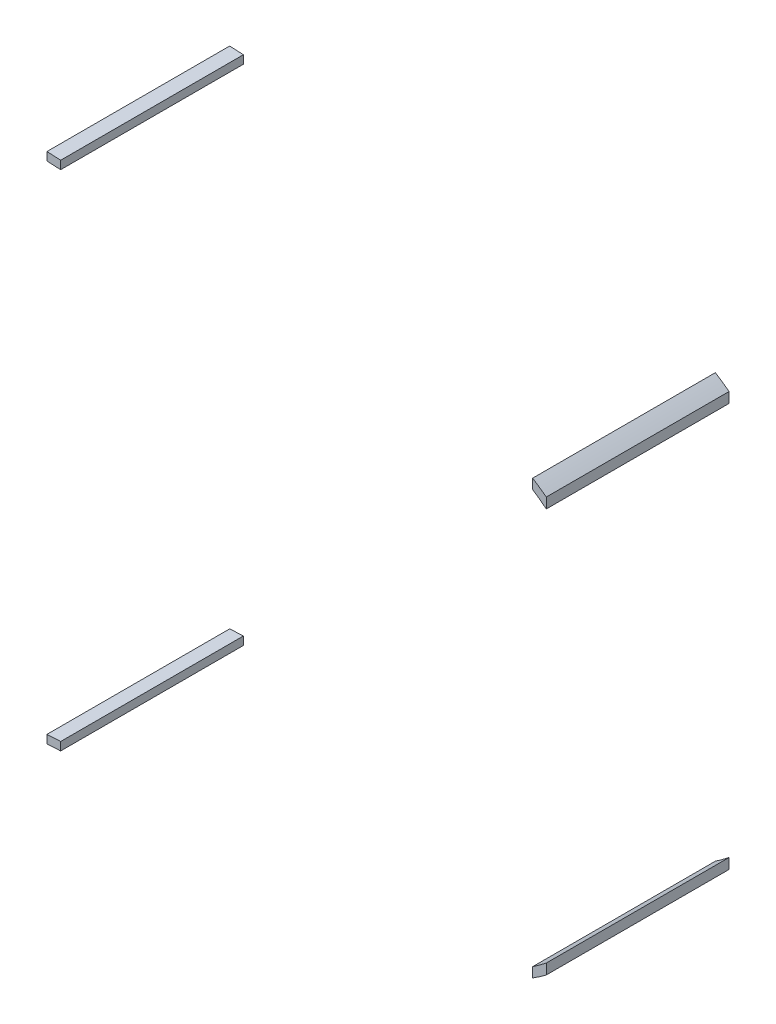
SolidWorks part; units mm, degrees
ref_plane "Front Plane" through (0, 0, 0) normal (0, 0, 1) x (1, 0, 0)
ref_plane "Top Plane" through (0, 0, 0) normal (0, 1, 0) x (1, 0, 0)
ref_plane "Right Plane" through (0, 0, 0) normal (1, 0, 0) x (0, 0, -1)
sketch "Sketch2" plane through (0, 0, 0) normal (0, 0, 1) x (1, 0, 0)
  line L7 (123.1026, -49.6697) -> (123.1026, -51.8155)
  line L19 (123.1026, 40.7834) -> (123.1026, 42.9292)
  line L20 (126.1026, 40.8584) -> (126.1026, 38.5895)
  line L21 (19.8026, -58.631) -> (19.8026, -60.4333)
  line L22 (19.8026, 49.7448) -> (16.8026, 49.8964)
  line L23 (19.8026, 49.7448) -> (19.8026, 51.5471)
  line L24 (16.8026, 51.6987) -> (19.8026, 51.5471)
  line L29 (16.8026, -58.7826) -> (16.8026, -60.5849)
  line L30 (16.8026, -60.5849) -> (19.8026, -60.4333)
  line L31 (126.1026, -49.7447) -> (126.1026, -47.4757)
  line L32 (19.8026, -58.631) -> (16.8026, -58.7826)
  line L33 (16.8026, 49.8964) -> (16.8026, 51.6987)
  spline S2 degree 3 poles (126.1026, 38.5895) (125.1269, 39.3562) (124.131, 40.0936) (123.1026, 40.7834) knots 0 0 0 0 0.241038 0.241038 0.241038 0.241038
  spline S3 degree 3 poles (123.1026, 42.9292) (124.1313, 42.2835) (125.128, 41.588) (126.1026, 40.8584) knots 0.757539 0.757539 0.757539 0.757539 1 1 1 1
  spline S12 degree 3 poles (123.1026, -51.8155) (124.1313, -51.1697) (125.128, -50.4742) (126.1026, -49.7447) knots 0.757539 0.757539 0.757539 0.757539 1 1 1 1
  spline S13 degree 3 poles (126.1026, -47.4757) (125.1269, -48.2425) (124.131, -48.9798) (123.1026, -49.6697) knots 0 0 0 0 0.241038 0.241038 0.241038 0.241038
  dimension "D5" = 3
  dimension "D6" = 3
extrude "Boss-Extrude1" add sketch "Sketch2" along normal blind 40
